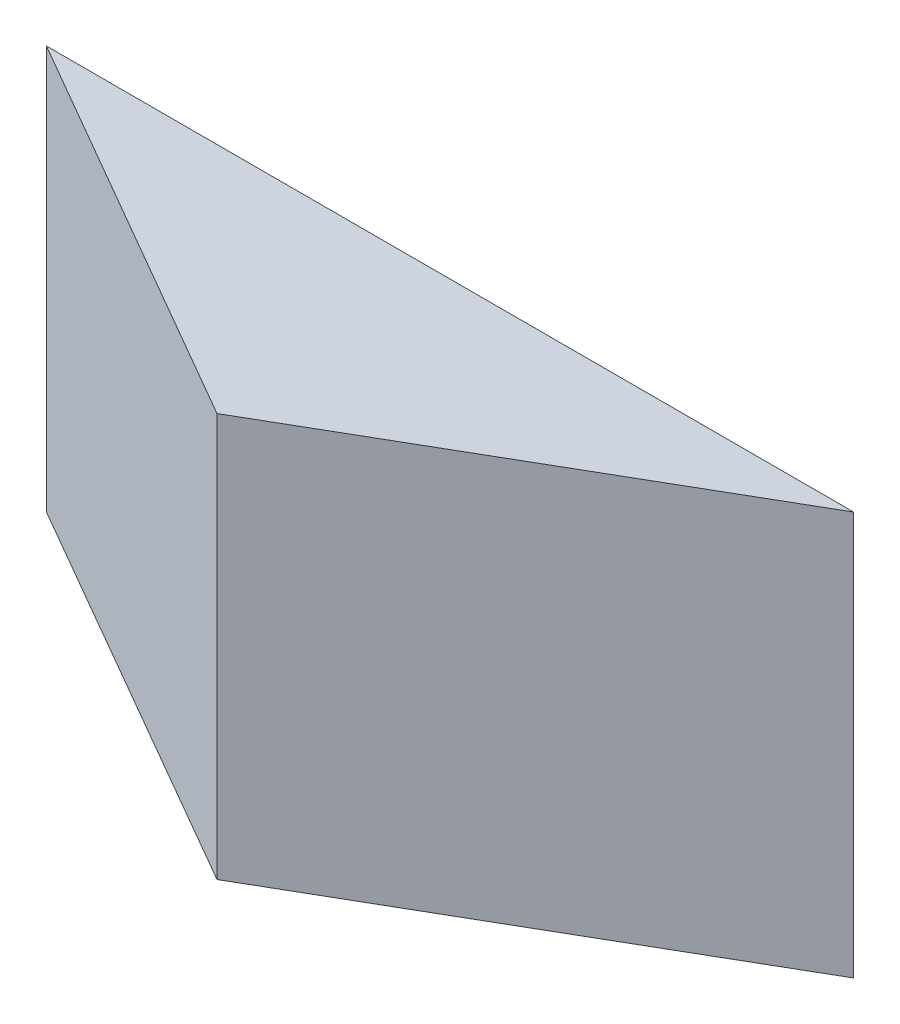
SolidWorks part; units mm, degrees
ref_plane "Front Plane" through (0, 0, 0) normal (0, 0, 1) x (1, 0, 0)
ref_plane "Top Plane" through (0, 0, 0) normal (0, 1, 0) x (1, 0, 0)
ref_plane "Right Plane" through (0, 0, 0) normal (1, 0, 0) x (0, 0, -1)
sketch "Sketch1" plane through (0, 0, 0) normal (0, 1, 0) x (1, 0, 0)
  line L0 (-321.9837, 0) -> (15777.1998, 0) construction
  line L1 (0, -321.9837) -> (0, 15777.1998) construction
  line L2 (0, 0) -> (12.7, 7.3323)
  line L3 (12.7, 7.3323) -> (-12.7, 7.3323)
  line L4 (0, 0) -> (-12.7, 7.3323)
  dimension "D1" = 25.4
  dimension "D2" = 12.7
  dimension "D3" = 30
  dimension "D4" = 30
extrude "Boss-Extrude1" add sketch "Sketch1" along normal blind 12.7
